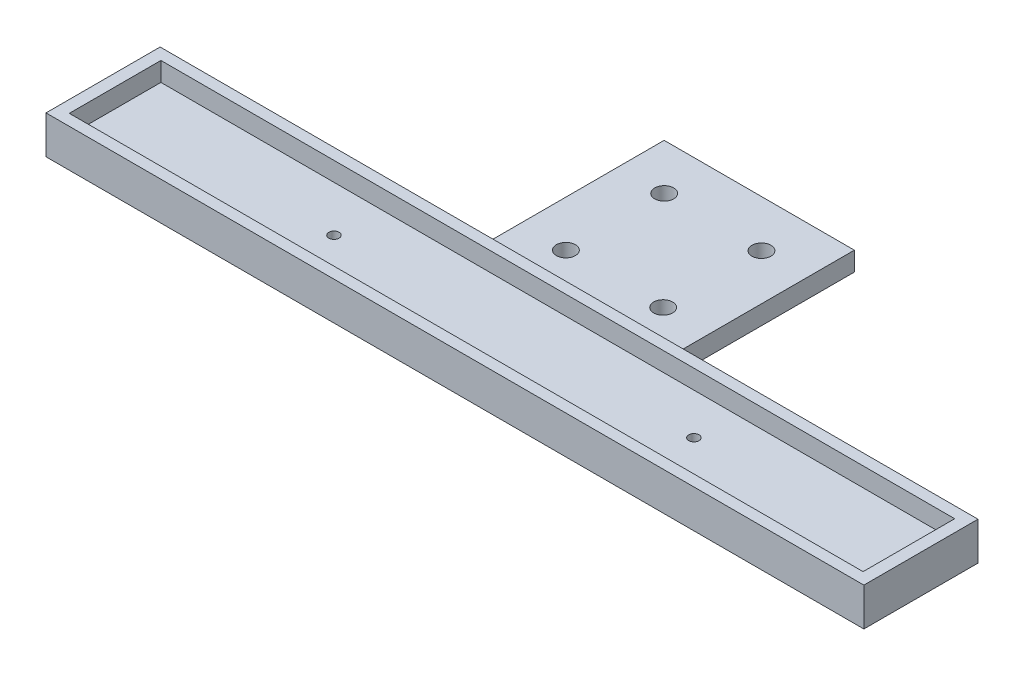
SolidWorks part; units mm, degrees
ref_plane "Front Plane" through (0, 0, 0) normal (0, 0, 1) x (1, 0, 0)
ref_plane "Top Plane" through (0, 0, 0) normal (0, 1, 0) x (1, 0, 0)
ref_plane "Right Plane" through (0, 0, 0) normal (1, 0, 0) x (0, 0, -1)
sketch "Sketch1" plane through (0, 0, 0) normal (0, 1, 0) x (1, 0, 0)
  line L1 (62.6, -7.225) -> (-62.6, -7.225)
  line L2 (62.6, -7.225) -> (62.6, 7.225)
  line L3 (62.6, 7.225) -> (-62.6, 7.225)
  line L4 (-62.6, -7.225) -> (-62.6, 7.225)
  line L5 (62.6, -7.225) -> (-62.6, 7.225) construction
  line L6 (62.6, 7.225) -> (-62.6, -7.225) construction
  line L7 (64.5, -9) -> (-64.5, -9)
  line L8 (64.5, -9) -> (64.5, 9)
  line L9 (64.5, 9) -> (-64.5, 9)
  line L10 (-64.5, -9) -> (-64.5, 9)
  line L11 (64.5, -9) -> (-64.5, 9) construction
  line L12 (64.5, 9) -> (-64.5, -9) construction
  point P0 (0, 0)
  point P6 (0, 0)
  dimension "D1" = 14.45
  dimension "D2" = 18
  dimension "D3" = 125.2
  dimension "D4" = 129
extrude "Boss-Extrude1" add sketch "Sketch1" along normal blind 3
sketch "Sketch2" plane through (0, 0, 0) normal (0, -1, 0) x (1, 0, 0)
  line L1 (64.5, 9) -> (-64.5, 9)
  line L2 (64.5, 9) -> (64.5, -9)
  line L3 (64.5, -9) -> (-64.5, -9)
  line L4 (-64.5, 9) -> (-64.5, -9)
  point P6 (0, 0)
  point P7 (0, 0)
  point P8 (0, 0)
  point P9 (0, -28.2518)
  point P11 (0, 0)
  point P12 (0, 0)
extrude "Boss-Extrude2" add sketch "Sketch2" along normal blind 3
sketch "Sketch4" plane through (0, 0, 0) normal (0, 1, 0) x (1, 0, 0)
  line L0 (62.6, -7.225) -> (62.6, 7.225) construction
  line L1 (62.6, 7.225) -> (-62.6, 7.225) construction
  line L2 (-62.6, 7.225) -> (-62.6, -7.225) construction
  circle A0 centre (27.97, 0.725) radius 0.81
  circle A1 centre (-28.08, 0) radius 0.81
  dimension "D4" = 1.62
  dimension "D5" = 1.62
  dimension "D1" = 34.63
  dimension "D2" = 6.5
  dimension "D3" = 34.52
extrude "Cut-Extrude1" cut sketch "Sketch4" against normal through all
sketch "Sketch5" plane through (0, -3, 0) normal (0, -1, 0) x (1, 0, 0)
  line L0 (-64.5, -9) -> (64.5, -9) construction
  line L1 (-15, -9) -> (15, -9)
  line L2 (-15, -9) -> (-15, -39)
  line L3 (-15, -39) -> (15, -39)
  line L4 (15, -9) -> (15, -39)
  circle A0 centre (7.75, -16.0927) radius 1.5
  circle A1 centre (7.7492, -31.5927) radius 1.5
  circle A2 centre (-7.75, -31.75) radius 1.5
  circle A3 centre (-7.7492, -16.25) radius 1.5
  point P8 (0, -39)
  point P11 (0, 0)
  point P17 (0, 0)
  point P18 (0, 0)
  point P19 (0, 0)
  dimension "D5" = 3
  dimension "D6" = 3
  dimension "D7" = 3
  dimension "D8" = 3
  dimension "D1" = 30
  dimension "D2" = 30
  dimension "D3" = 15.5
  dimension "D4" = 15.5
  dimension "D9" = 15.5
  dimension "D10" = 15.5
  dimension "D11" = 7.25
  dimension "D12" = 7.25
extrude "Boss-Extrude4" add sketch "Sketch5" against normal blind 3
